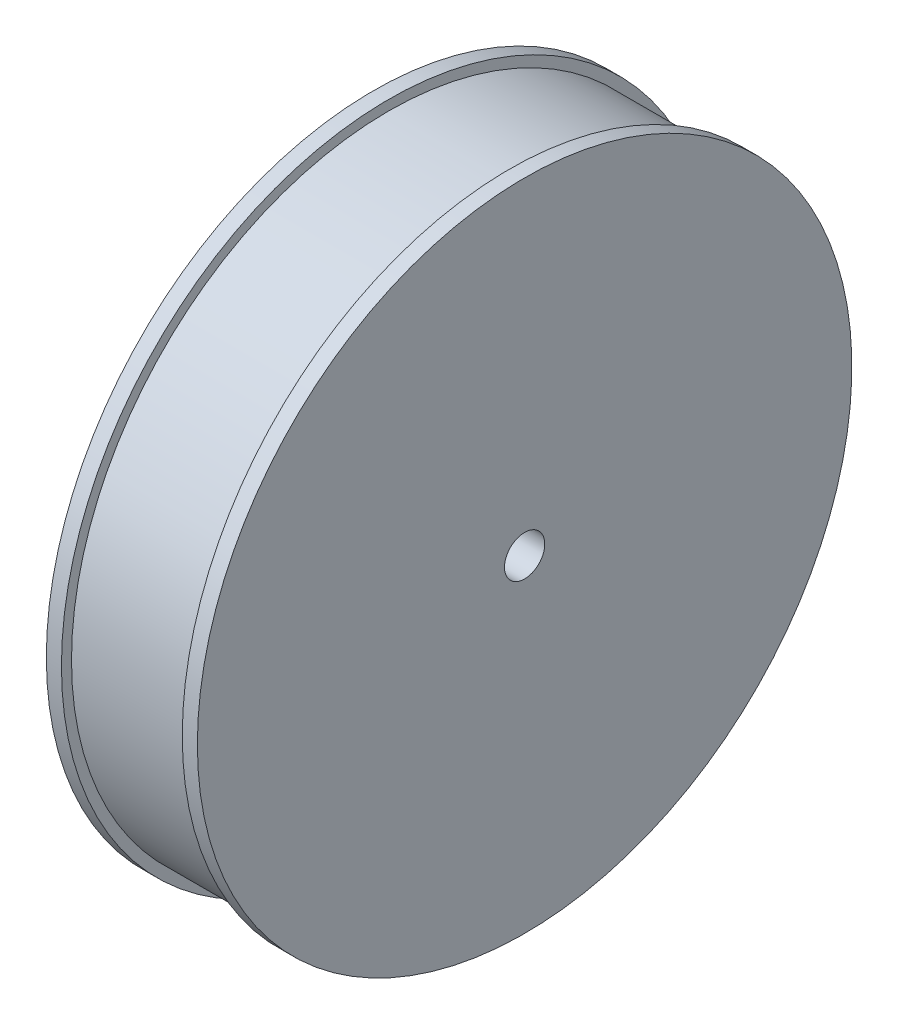
SolidWorks part; units mm, degrees
ref_plane "Front" through (0, 0, 0) normal (0, 0, 1) x (1, 0, 0)
ref_plane "Top" through (0, 0, 0) normal (0, 1, 0) x (1, 0, 0)
ref_plane "Right" through (0, 0, 0) normal (1, 0, 0) x (0, 0, -1)
sketch "Sketch1" plane through (0, 0, 0) normal (0, 0, 1) x (1, 0, 0)
  line L1 (-15, 0) -> (15, 0) construction
  line L2 (12, 65) -> (15, 65)
  line L3 (15, 4) -> (15, 65)
  line L6 (12, 65) -> (12, 63)
  line L7 (-12, 63) -> (12, 63)
  line L8 (0, -50) -> (0, 50) construction
  line L9 (-15, 4) -> (-15, 65)
  line L10 (-12, 65) -> (-15, 65)
  line L11 (-12, 65) -> (-12, 63)
  line L13 (-15, 0) -> (15, 0) construction
  line L15 (-15, 4) -> (15, 4)
  point P6 (0, 0)
  dimension "D1" = 15
  dimension "D2" = 65
  dimension "D3" = 3
  dimension "D4" = 2
  dimension "D5" = 4
revolve "Revolve1" add sketch "Sketch1" angle 360 about L1
